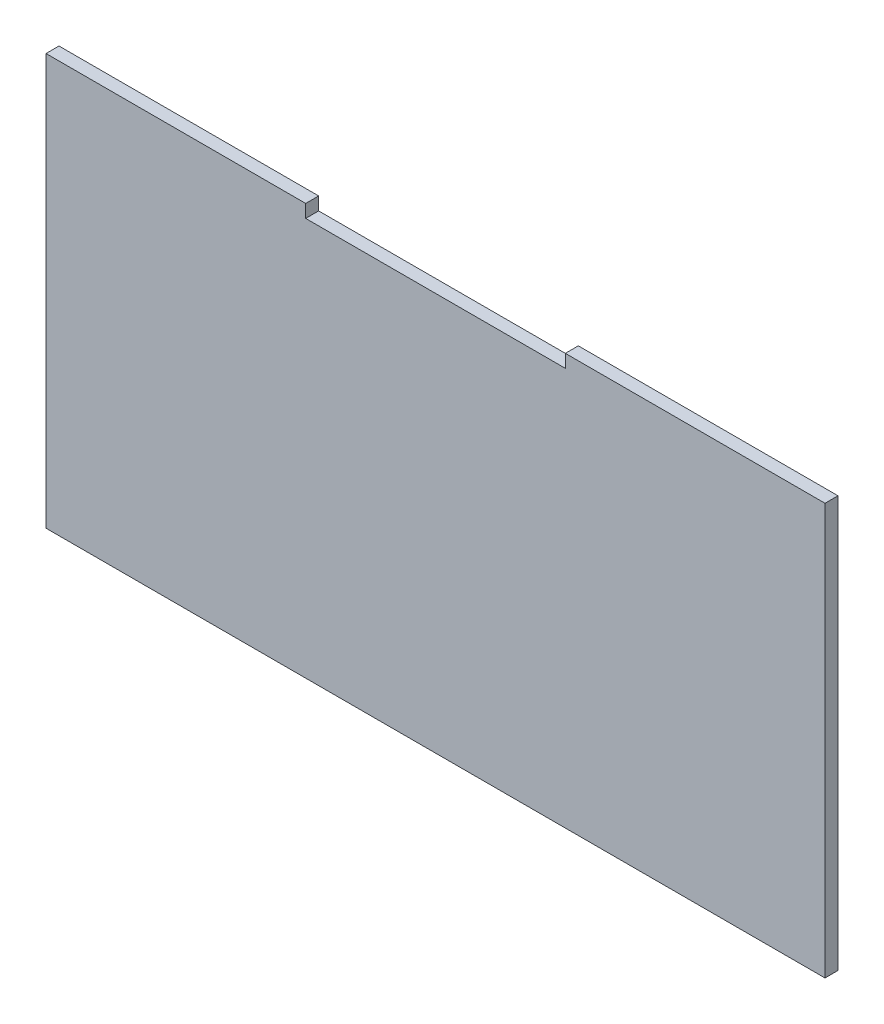
SolidWorks part; units mm, degrees
material "Acrylic (Medium-high impact)"
ref_plane "Front Plane" through (0, 0, 0) normal (0, 0, 1) x (1, 0, 0)
ref_plane "Top Plane" through (0, 0, 0) normal (0, 1, 0) x (1, 0, 0)
ref_plane "Right Plane" through (0, 0, 0) normal (1, 0, 0) x (0, 0, -1)
sketch "Sketch1" plane through (0, 0, 0) normal (0, 0, 1) x (1, 0, 0)
  line L0 (-30, 44.5) -> (30, 44.5)
  line L1 (90, 47.5) -> (30, 47.5)
  line L2 (90, 47.5) -> (90, -47.5)
  line L3 (90, -47.5) -> (-90, -47.5)
  line L4 (-90, 47.5) -> (-90, -47.5)
  line L7 (-30, 47.5) -> (-30, 44.5)
  line L8 (30, 47.5) -> (30, 44.5)
  line L9 (-30, 47.5) -> (-90, 47.5)
  line L10 (0, 44.5) -> (0, 47.5) construction
  point P0 (0, 0)
  dimension "D1" = 95
  dimension "D2" = 180
  dimension "D3" = 3
  dimension "D4" = 60
  dimension "D5" = 60
extrude "Boss-Extrude1" add sketch "Sketch1" along normal blind 3
